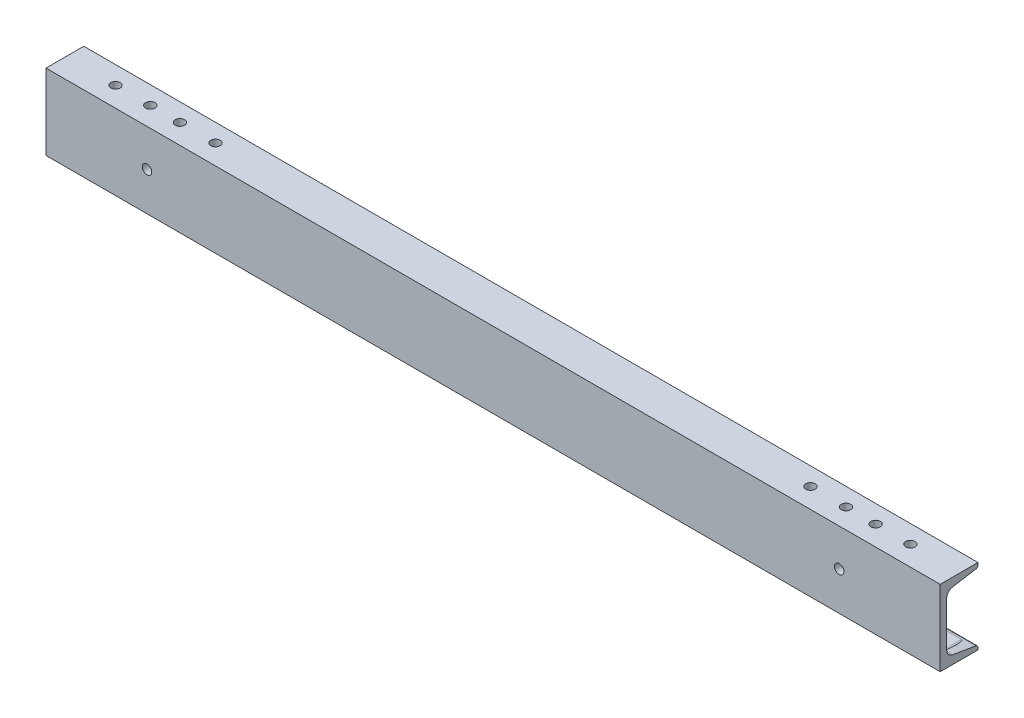
SolidWorks part; units mm, degrees
material "Plain Carbon Steel"
ref_plane "Front Plane" through (0, 0, 0) normal (0, 0, 1) x (1, 0, 0)
ref_plane "Top Plane" through (0, 0, 0) normal (0, 1, 0) x (1, 0, 0)
ref_plane "Right Plane" through (0, 0, 0) normal (1, 0, 0) x (0, 0, -1)
sketch "Sketch1" plane through (0, 0, 0) normal (0, 1, 0) x (1, 0, 0)
  line L0 (-450, 0) -> (450, 0)
  dimension "D1" = 900
other "Structural Member1"
ref_plane "Plane1" through (-450, 0, 0) normal (1, 0, 0) x (0, 0, -1)
sketch "Sketch11" plane through (-450, 0, 0) normal (1, 0, 0) x (0, 0, -1)
  line L0 (0, -38.1) -> (0, 38.1)
  line L1 (0, 38.1) -> (38.0492, 38.1)
  line L2 (0, -38.1) -> (38.0492, -38.1)
  line L5 (31.75, -31.1658) -> (6.35, -31.1658) construction
  line L6 (0, 0) -> (6.5532, 0) construction
  line L12 (6.5532, 22.7314) -> (6.5532, -22.7314)
  line L15 (38.0492, 38.1) -> (38.0492, 35.9423)
  line L16 (38.0492, -38.1) -> (38.0492, -35.9423)
  line L17 (12.2837, 29.4961) -> (35.9268, 33.4369)
  line L18 (12.2837, -29.4961) -> (35.9268, -33.4369)
  arc A9 (6.5532, -22.7314) -> (12.2837, -29.4961) centre (13.4112, -22.7314) ccw
  arc A10 (6.5532, 22.7314) -> (12.2837, 29.4961) centre (13.4112, 22.7314) cw
  arc A11 (38.0492, 35.9423) -> (35.9268, 33.4369) centre (35.5092, 35.9423) cw
  arc A12 (38.0492, -35.9423) -> (35.9268, -33.4369) centre (35.5092, -35.9423) ccw
  point P4 (38.0492, 33.7907)
  point P5 (38.0492, -33.7907)
  point P6 (3.2766, 0)
  point P7 (19.0246, 38.1)
  point P12 (19.0246, -38.1)
  point P13 (0, 0)
  dimension "RI" = 6.858
  dimension "D2" = 9.463
  dimension "RA" = 2.54
  dimension "Depth" = 76.2
  dimension "BF" = 38.0492
  dimension "TW" = 6.5532
  dimension "flange" = 2.1577
  dimension "TF" = 6.9342
sketch "Sketch12" plane through (0, 0, 0) normal (0, 1, 0) x (1, 0, 0)
  line L0 (-412.5239, 20) -> (413.742, 20) construction
  line L1 (-450, 0) -> (450, 0) construction
  line L2 (0, 0) -> (0, 45.9021) construction
  line L3 (-450, 38.0492) -> (-450, 0) construction
  circle A0 centre (-425, 20) radius 4.7625
  circle A1 centre (425, 20) radius 4.7625
  dimension "D2" = 9.525
  dimension "D1" = 20
  dimension "D3" = 25
extrude "Cut-Extrude1" cut sketch "Sketch12" against normal through all
sketch "Sketch15" plane through (0, 0, -6.5532) normal (0, 0, -1) x (-1, 0, 0)
  line L0 (-425, -21.1359) -> (-425, -40.4286) construction
  line L1 (-375.1366, -28.1) -> (-474.8634, -28.1) construction
  line L2 (-450, -38.1) -> (450, -38.1) construction
  line L3 (-412.5, -28.1) -> (-437.5, -28.1) construction
  line L4 (-412.5, -33.1) -> (-437.5, -33.1)
  line L5 (-412.5, -23.1) -> (-437.5, -23.1)
  line L6 (0, 0) -> (0, -58.1771) construction
  line L7 (412.5, -28.1) -> (437.5, -28.1) construction
  line L8 (412.5, -33.1) -> (437.5, -33.1)
  line L9 (412.5, -23.1) -> (437.5, -23.1)
  arc A0 (-412.5, -33.1) -> (-412.5, -23.1) centre (-412.5, -28.1) ccw
  arc A1 (-437.5, -23.1) -> (-437.5, -33.1) centre (-437.5, -28.1) ccw
  arc A2 (412.5, -33.1) -> (412.5, -23.1) centre (412.5, -28.1) cw
  arc A3 (437.5, -23.1) -> (437.5, -33.1) centre (437.5, -28.1) cw
  ellipse E0 centre (-425, -30.7822) end of major axis (-429.7625, -30.7822) minor radius 0.7938 construction
  point P0 (-425, -30.7822)
  point P11 (-425, -28.1)
  point P16 (-425, -28.1)
  point P26 (425, -28.1)
  dimension "D2" = 5
  dimension "D1" = 10
  dimension "D3" = 25
extrude "Cut-Extrude2" cut sketch "Sketch15" along normal blind 40
sketch "Sketch16" plane through (0, 0, 0) normal (0, 1, 0) x (1, 0, 0)
  line L0 (0, -46.4014) -> (0, 86.4014) construction
  line L1 (-394.0256, 20) -> (394.0256, 20) construction
  line L2 (450, 0) -> (-450, 0) construction
  circle A0 centre (-335.2, 20) radius 4.7625
  circle A1 centre (-299.4, 20) radius 4.7625
  circle A2 centre (299.4, 20) radius 4.7625
  circle A3 centre (335.2, 20) radius 4.7625
  circle A4 centre (-365, 20) radius 4.7625
  circle A5 centre (-400, 20) radius 4.7625
  circle A6 centre (365, 20) radius 4.7625
  circle A7 centre (400, 20) radius 4.7625
  point P5 (0, 20)
  point P6 (0, 20)
  dimension "D2" = 9.525
  dimension "D1" = 20
  dimension "D3" = 335.2
  dimension "D4" = 35.8
  dimension "D5" = 35
  dimension "D6" = 400
extrude "Cut-Extrude3" cut sketch "Sketch16" along normal through all
sketch "Sketch19" plane through (0, 0, 0) normal (0, 0, 1) x (1, 0, 0)
  circle A0 centre (-348.3375, 0.6) radius 4.7625 construction
  circle A1 centre (348.3375, 0.6) radius 4.7625 construction
  circle A2 centre (-348.3375, 0.6) radius 4.7625
  circle A3 centre (348.3375, 0.6) radius 4.7625
extrude "Cut-Extrude4" cut sketch "Sketch19" against normal through all
